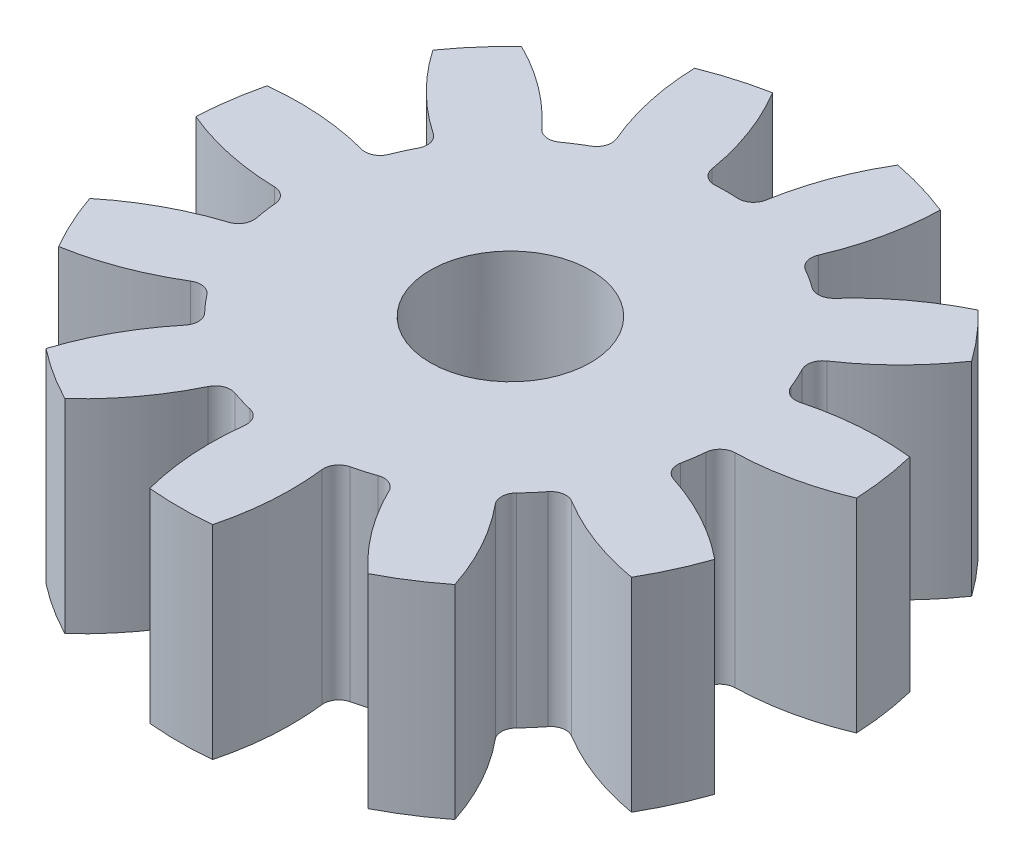
SolidWorks part; units mm, degrees
ref_plane "Plano frontal" through (0, 0, 0) normal (0, 0, 1) x (1, 0, 0)
ref_plane "Plano superior" through (0, 0, 0) normal (0, 1, 0) x (1, 0, 0)
ref_plane "Plano direito" through (0, 0, 0) normal (1, 0, 0) x (0, 0, -1)
sketch "Sketch10" plane through (0, 0, 0) normal (0, 1, 0) x (1, 0, 0)
  circle A0 centre (0, 0) radius 11 construction
  circle A1 centre (0, 0) radius 13
  circle A2 centre (0, 0) radius 8.5
  dimension "D1" = 22
  dimension "D2" = 26
  dimension "D3" = 17
extrude "Boss-Extrude1" add sketch "Sketch10" along normal blind 8 contours A1
sketch "Sketch11" plane through (0, 8, 0) normal (0, 1, 0) x (1, 0, 0)
  line L0 (0, 0) -> (0, 13) construction
  line L1 (-1.5655, 10.888) -> (1.5655, 10.888) construction
  line L2 (0, 0) -> (-0.986, 8.4426) construction
  line L3 (0, 6.587) -> (-2.6089, 13.7548) construction
  line L4 (0, 0) -> (3.6625, 12.4734) construction
  line L5 (1.5655, 10.888) -> (4.5696, 10.006) construction
  circle A0 centre (0, 0) radius 11 construction
  arc A1 (-3.0631, 13.6608) -> (-0.986, 8.4426) centre (-11.7325, 7.1875) cw
  circle A2 centre (0, 0) radius 13 construction
  arc A3 (3.0631, 13.6608) -> (0.986, 8.4426) centre (11.7325, 7.1875) ccw
  circle A4 centre (0, 0) radius 8.5 construction
  arc A5 (0.986, 8.4426) -> (-0.986, 8.4426) centre (0, 0) ccw
  circle A10 centre (0, 0) radius 14
  arc A11 (3.0631, 13.6608) -> (-3.0631, 13.6608) centre (0, 0) ccw
  dimension "D1" = 22
  dimension "D2" = 1
  dimension "D3" = 20
  dimension "D4" = 16.364
extrude "Cut-Extrude1" cut sketch "Sketch11" against normal through all
fillet "Fillet1" radius 0.6 2 edges at (0.986, 4, -8.4426) (-0.986, 4, -8.4426)
pattern_circular "CirPattern1" count 11 over 360 about axis through (0, 0, 0) along (0, 1, 0) of "Cut-Extrude1", "Fillet1"
sketch "Sketch12" plane through (0, 8, 0) normal (0, 1, 0) x (1, 0, 0)
  circle A0 centre (0, 0) radius 3.15
  dimension "D1" = 6.3
extrude "Cut-Extrude2" cut sketch "Sketch12" against normal offset from surface (6 mm away) 2 up to face at (0, 0, 0)
sketch "Sketch13" plane through (0, 2, 0) normal (0, 1, 0) x (1, 0, 0)
  line L0 (-0.375, 3.1276) -> (-0.375, -3.1276)
  line L1 (0, 0) -> (0, 3.15) construction
  line L2 (0.375, 3.1276) -> (0.375, -3.1276)
  circle A0 centre (0, 0) radius 3.15 construction
  arc A1 (-0.375, -3.1276) -> (0.375, -3.1276) centre (0, 0) ccw
  arc A2 (0.375, 3.1276) -> (-0.375, 3.1276) centre (0, 0) ccw
  dimension "D1" = 0.75
extrude "Boss-Extrude2" add sketch "Sketch13" along normal blind 0.75
